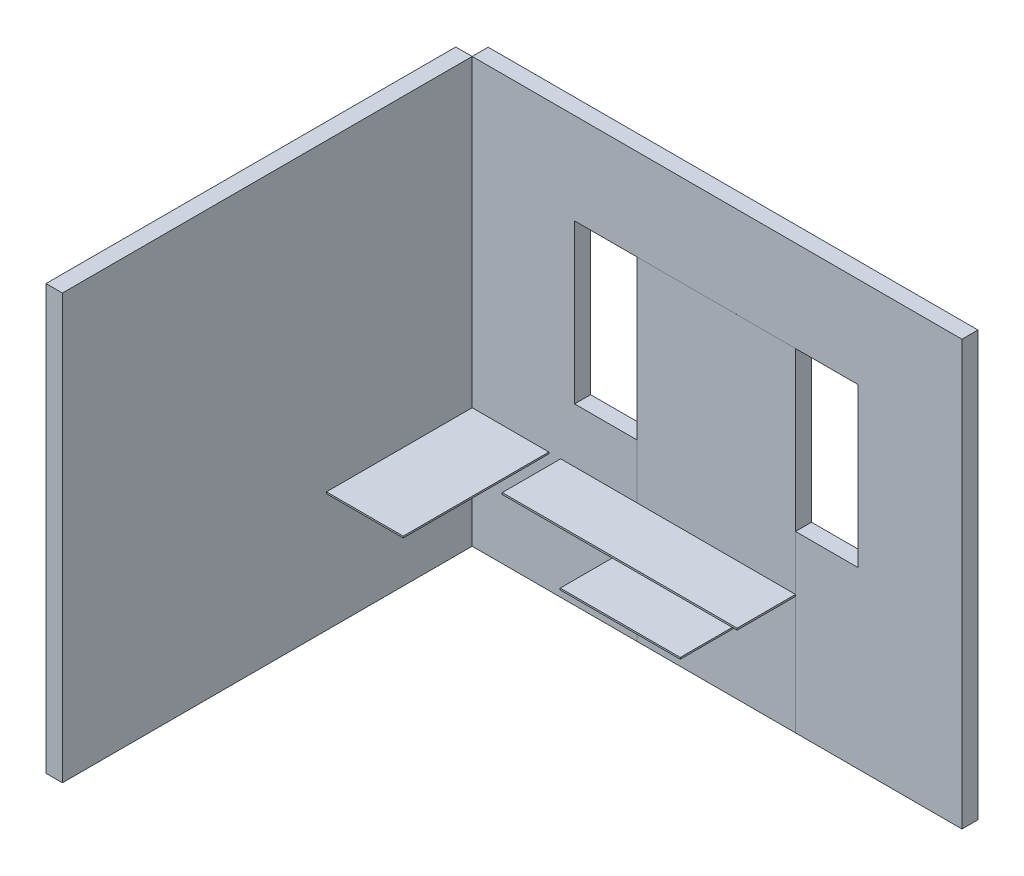
SolidWorks part; units mm, degrees
ref_plane "Plano frontal" through (0, 0, 0) normal (0, 0, 1) x (1, 0, 0)
ref_plane "Plano superior" through (0, 0, 0) normal (0, 1, 0) x (1, 0, 0)
ref_plane "Plano direito" through (0, 0, 0) normal (1, 0, 0) x (0, 0, -1)
sketch "Esboço6" plane through (0, 0, 0) normal (0, 0, 1) x (1, 0, 0)
  line L1 (0, 0) -> (3060, 0)
  line L2 (0, 0) -> (0, 2650)
  line L3 (0, 2650) -> (3060, 2650)
  line L4 (3060, 0) -> (3060, 2650)
extrude "Ressalto-extrusão2" add sketch "Esboço6" along normal blind 100
sketch "Esboço7" plane through (0, 0, 100) normal (0, 0, 1) x (1, 0, 0)
  line L2 (2020, 2080) -> (2020, 1090)
  line L3 (640, 2080) -> (640, 1090)
  line L4 (640, 2080) -> (1030, 2080)
  line L5 (1030, 2080) -> (1030, 1090)
  line L6 (1030, 1090) -> (640, 1090)
  line L7 (2020, 1090) -> (2410, 1090)
  line L8 (2410, 1090) -> (2410, 2080)
  line L9 (2410, 2080) -> (2020, 2080)
extrude "Corte-extrusão1" cut sketch "Esboço7" against normal blind 749
sketch "Esboço8" plane through (0, 0, 100) normal (0, 0, 1) x (1, 0, 0)
  line L0 (0, 2650) -> (-102.4312, 2650)
  line L1 (-102.4312, 2650) -> (-102.4312, 0)
  line L2 (-102.4312, 0) -> (0, 0)
  line L3 (0, 0) -> (0, 2650)
extrude "Ressalto-extrusão3" add sketch "Esboço8" along normal blind 2560 separate body
sketch "Esboço9" plane through (0, 0, 100) normal (0, 0, 1) x (1, 0, 0)
  line L1 (0, 0) -> (0, 2650) construction
  line L2 (0, 739.3899) -> (479.152, 739.3899)
  line L3 (479.152, 739.3899) -> (479.152, 749.3899)
  line L4 (479.152, 749.3899) -> (0, 749.3899)
  line L5 (0, 749.3899) -> (0, 739.3899)
extrude "Ressalto-extrusão5" add sketch "Esboço9" along normal blind 910 separate body
sketch "Esboço12" plane through (0, 0, 100) normal (0, 0, 1) x (1, 0, 0)
  line L1 (552.8669, 749.3899) -> (2020, 749.3899)
  line L2 (2020, 749.3899) -> (2020, 738.5475)
  line L3 (552.8669, 738.7437) -> (552.8669, 749.3899)
  line L4 (2020, 738.5475) -> (552.8669, 738.7437)
extrude "Ressalto-extrusão7" add sketch "Esboço12" along normal blind 365
sketch "Esboço13" plane through (0, 0, 100) normal (0, 0, 1) x (1, 0, 0)
  line L0 (1030, 2080) -> (2020, 2080)
  line L1 (2020, 2080) -> (2020, 749.3899)
  line L2 (2020, 749.3899) -> (552.8669, 749.3899) construction
  line L3 (1030, 2080) -> (1030, 749.3899)
  line L4 (1030, 749.3899) -> (2020, 749.3899)
  line L5 (2020, 738.5475) -> (2020, 0)
  line L6 (0, 0) -> (3060, 0) construction
  line L7 (2020, 0) -> (1030, 0)
  line L8 (1030, 0) -> (1030, 738.6799)
  line L9 (552.8669, 738.7437) -> (2020, 738.5475) construction
  line L10 (1030, 738.6799) -> (2020, 738.5475)
extrude "Ressalto-extrusão8" add sketch "Esboço13" along normal blind 0.01
sketch "Esboço14" plane through (0, 0, 100.01) normal (0, 0, 1) x (1, 0, 0)
  line L0 (1150, 648.6137) -> (1900, 648.6137)
  line L4 (1900, 648.6137) -> (1900, 638.6137)
  line L5 (1900, 638.6137) -> (1150, 638.6137)
  line L6 (1150, 638.6137) -> (1150, 648.6137)
extrude "Ressalto-extrusão9" add sketch "Esboço14" along normal blind 600
